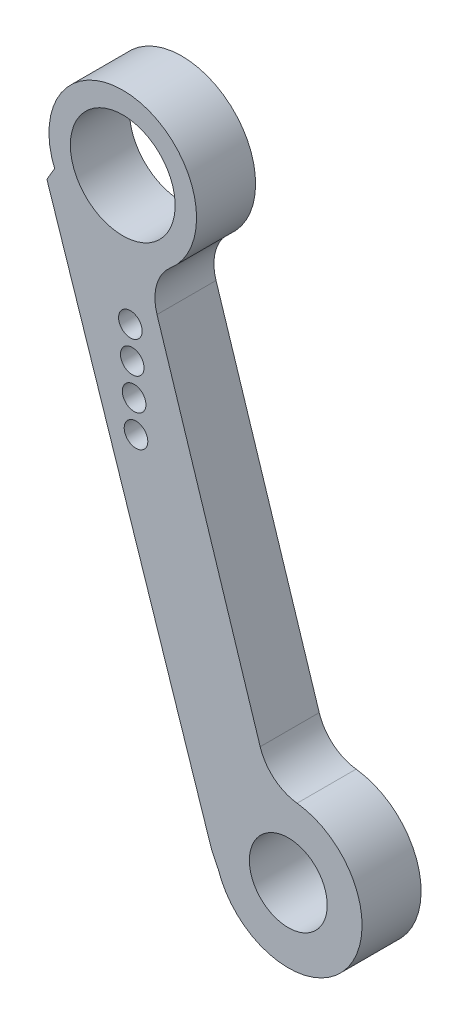
SolidWorks part; units mm, degrees
material "PLA"
ref_plane "Front Plane" through (0, 0, 0) normal (0, 0, 1) x (1, 0, 0)
ref_plane "Top Plane" through (0, 0, 0) normal (0, 1, 0) x (1, 0, 0)
ref_plane "Right Plane" through (0, 0, 0) normal (1, 0, 0) x (0, 0, -1)
ref_plane "Plane1" through (0, 0, 4) normal (0, 0, 1) x (1, 0, 0)
sketch "Sketch1" plane through (0, 0, 4) normal (0, 0, 1) x (1, 0, 0)
  line L0 (4.3612, 84.5098) -> (3.8387, 83.6229)
  line L1 (3.8387, 83.6229) -> (15.0111, 49.8307)
  line L2 (15.0111, 49.8307) -> (15.4551, 48.9286)
  line L3 (18.2905, 57.5508) -> (11.2998, 79.4142)
  arc A0 (15.4551, 48.9286) -> (20.7905, 55.4858) centre (20.1946, 50.5214) ccw
  arc A1 (20.7905, 55.4858) -> (18.2905, 57.5508) centre (21.148, 58.4644) cw
  arc A2 (11.2998, 79.4142) -> (12.2156, 82.6148) centre (14.1573, 80.3279) cw
  arc A3 (12.2156, 82.6148) -> (4.3612, 84.5098) centre (8.9794, 86.4262) ccw
  circle A4 centre (20.1946, 50.5214) radius 2.6375
  circle A5 centre (8.9794, 86.4262) radius 3.55
  circle A6 centre (9.4944, 77.9418) radius 0.8
  circle A7 centre (9.6216, 75.8456) radius 0.8
  circle A8 centre (9.7488, 73.7495) radius 0.8
  circle A9 centre (9.8761, 71.6534) radius 0.8
extrude "Boss-Extrude1" add sketch "Sketch1" against normal blind 4
